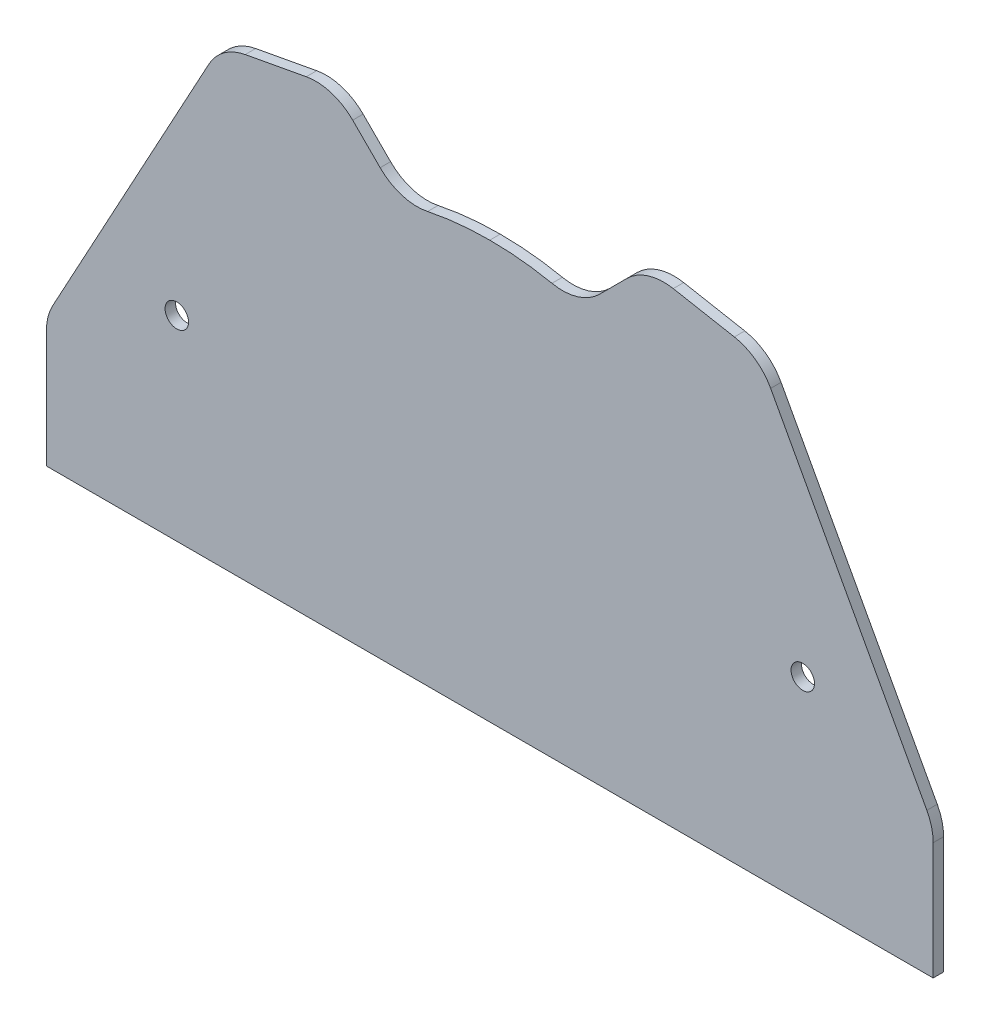
SolidWorks part; units mm, degrees
ref_plane "Alzado" through (0, 0, 0) normal (0, 0, 1) x (1, 0, 0)
ref_plane "Planta" through (0, 0, 0) normal (0, 1, 0) x (1, 0, 0)
ref_plane "Vista lateral" through (0, 0, 0) normal (1, 0, 0) x (0, 0, -1)
sketch "Croquis1" plane through (0, 0, 0) normal (0, 0, 1) x (1, 0, 0)
  line L0 (-85, 0) -> (85, 0)
  line L1 (-85, 0) -> (-85, 25)
  line L2 (-30, 90.5) -> (-51.5672, 86.5)
  line L3 (-30, 90.5) -> (-17, 77.5)
  line L4 (0, 0) -> (0, 80) construction
  line L5 (17, 80) -> (-17, 80) construction
  line L6 (-51.5672, 86.5) -> (-85, 25)
  line L8 (-17, 80) -> (-17, 71.3257) construction
  line L9 (17, 80) -> (17, 71.3257) construction
  line L11 (51.5672, 86.5) -> (85, 25)
  line L12 (30, 90.5) -> (17, 77.5)
  line L13 (30, 90.5) -> (51.5672, 86.5)
  line L14 (85, 0) -> (85, 25)
  arc A0 (-17, 77.5) -> (0, 80) centre (-0.1868, 22.2203) cw
  arc A1 (17, 77.5) -> (0, 80) centre (0.1868, 22.2203) ccw
  circle A2 centre (-60, 37.5) radius 2.25
  circle A3 centre (60, 37.5) radius 2.25
  dimension "D11" = 4.5
  dimension "D1" = 85
  dimension "D2" = 25
  dimension "D3" = 80
  dimension "D4" = 17
  dimension "D5" = 4
  dimension "D6" = 13
  dimension "D7" = 13
  dimension "D8" = 70
  dimension "D9" = 37.5
  dimension "D10" = 25
  dimension "D12" = 2.5
extrude "Saliente-Extruir1" add sketch "Croquis1" along normal blind 2
fillet "Redondeo1" radius 10 8 edges at (-85, 25, 1) (85, 25, 1) (51.5672, 86.5, 1) (30, 90.5, 1) (17, 77.5, 1) (-17, 77.5, 1) (-30, 90.5, 1) (-51.5672, 86.5, 1)
